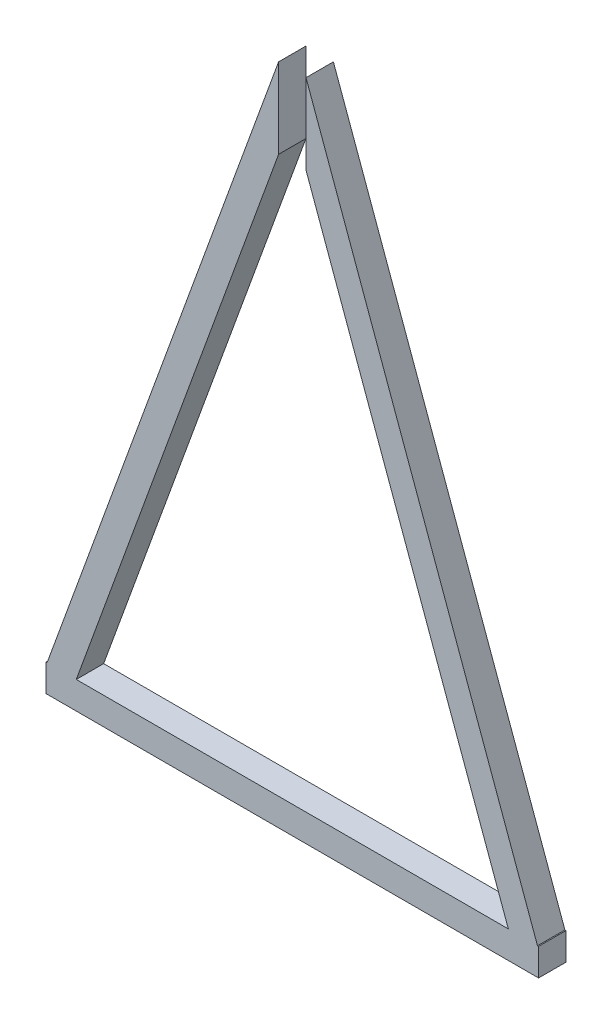
SolidWorks part; units mm, degrees
ref_plane "Alzado" through (0, 0, 0) normal (0, 0, 1) x (1, 0, 0)
ref_plane "Planta" through (0, 0, 0) normal (0, 1, 0) x (1, 0, 0)
ref_plane "Vista lateral" through (0, 0, 0) normal (1, 0, 0) x (0, 0, -1)
sketch "Croquis1" plane through (0, 0, 0) normal (0, 0, 1) x (1, 0, 0)
  line L1 (0, 0) -> (1370, 0)
  line L2 (0, 0) -> (0, 76.2)
  line L3 (0, 76.2) -> (1370, 76.2)
  line L4 (1370, 0) -> (1370, 76.2)
  dimension "D1" = 1370
  dimension "D2" = 76.2
extrude "Saliente-Extruir1" add sketch "Croquis1" along normal blind 76.2
sketch "Croquis2" plane through (0, 0, 76.2) normal (0, 0, 1) x (1, 0, 0)
  line L0 (685, 76.2) -> (685, 1876.2) construction
  line L1 (1370, 76.2) -> (0, 76.2) construction
  line L2 (723.1, 1845.4232) -> (723.1, 1622.6293)
  line L3 (723.1, 1622.6293) -> (1285.9542, 76.2)
  line L4 (723.1, 1845.4232) -> (1367.0446, 76.2)
  line L5 (705.0487, 1895.0186) -> (1357.5588, 102.2619) construction
  line L6 (2.9554, 76.2) -> (84.0458, 76.2)
  line L7 (646.9, 1845.4232) -> (804.0214, 1788.2356) construction
  line L8 (633.4441, 1868.9567) -> (1285.9542, 76.2) construction
  line L9 (1285.9542, 76.2) -> (1367.0446, 76.2)
  line L10 (646.9, 1845.4232) -> (2.9554, 76.2)
  line L11 (646.9, 1622.6293) -> (84.0458, 76.2)
  line L12 (646.9, 1845.4232) -> (646.9, 1622.6293)
  line L13 (2.9554, 76.2) -> (263.1533, -18.5043) construction
  dimension "D1" = 1800
  dimension "D2" = 38.1
  dimension "D3" = 20
  dimension "D5" = 76.2
  dimension "D6" = 70
  dimension "D7" = 20
  dimension "D4" = 76.2
extrude "Saliente-Extruir2" add sketch "Croquis2" against normal up to surface (76.2 mm away) up to face at (685, 38.1, 0)
